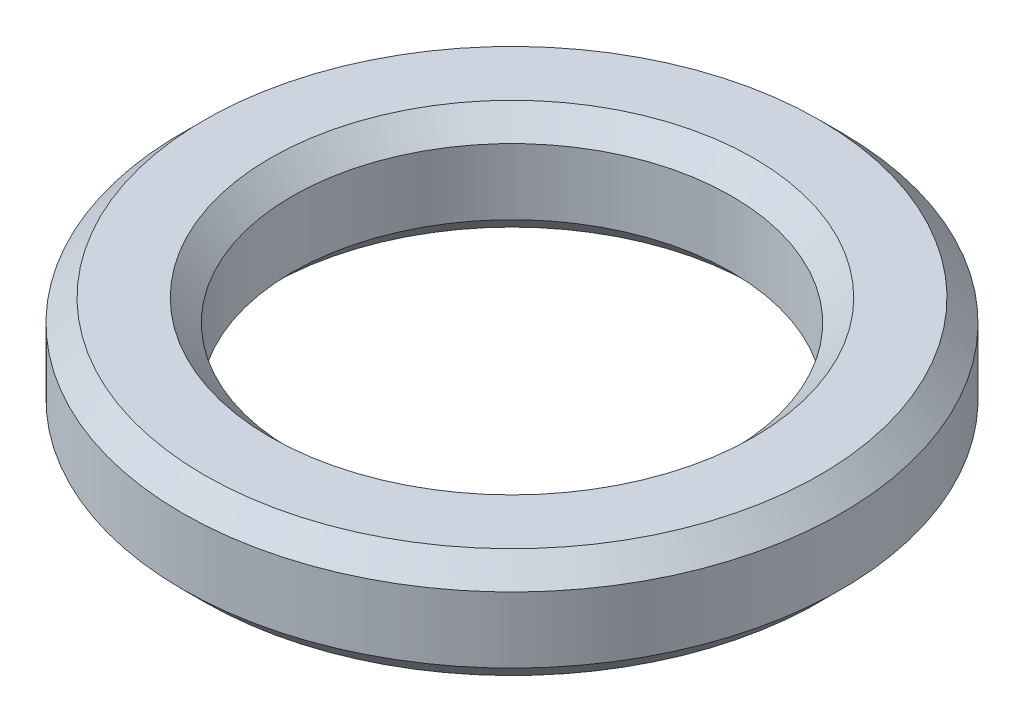
SolidWorks part; units mm, degrees
ref_plane "Front Plane" through (0, 0, 0) normal (0, 0, 1) x (1, 0, 0)
ref_plane "Top Plane" through (0, 0, 0) normal (0, 1, 0) x (1, 0, 0)
ref_plane "Right Plane" through (0, 0, 0) normal (1, 0, 0) x (0, 0, -1)
sketch "Sketch1" plane through (0, 0, 0) normal (0, 1, 0) x (1, 0, 0)
  circle A0 centre (0, 0) radius 10
  dimension "D1" = 20
extrude "Extrude-Thin1" add sketch "Sketch1" along normal blind 5 thin
chamfer "Chamfer1" distance 1 angle 45 4 edges at (0, 0, 10) (15, 0, 0) (0, 5, 10) (15, 5, 0)
